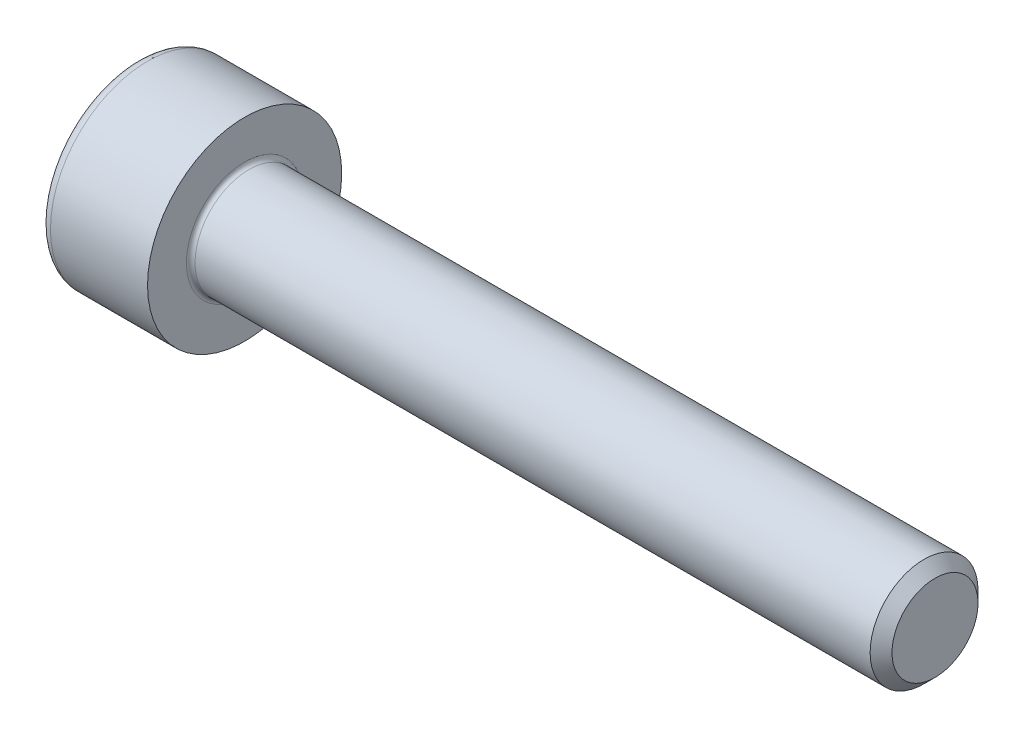
SolidWorks part; units mm, degrees
ref_plane "Plane1" through (0, 0, 0) normal (0, 0, 1) x (1, 0, 0)
ref_plane "Plane2" through (0, 0, 0) normal (0, 1, 0) x (1, 0, 0)
ref_plane "Plane3" through (0, 0, 0) normal (1, 0, 0) x (0, 0, -1)
sketch "BodySke" plane through (0, 0, 0) normal (0, 0, 1) x (1, 0, 0)
  line L0 (0, 0) -> (0, 2.25)
  line L1 (0, 2.25) -> (2.5, 2.25)
  line L2 (2.5, 2.25) -> (2.5, 1.25)
  line L3 (2.5, 1.25) -> (18.2465, 1.25)
  line L4 (18.5, 0.9965) -> (18.5, 0)
  line L5 (18.5, 0) -> (0, 0)
  line L6 (-31.75, 0) -> (127, 0) construction
  line L8 (18.5, 0.9965) -> (18.2465, 1.25)
  line L10 (18.5, -0.9965) -> (18.2465, -1.25) construction
  line L11 (2.95, 9.525) -> (2.95, 3.175) construction
  line L12 (2.5, 9.525) -> (2.5, 3.175) construction
  line L13 (-41.5, 9.525) -> (-41.5, 3.175) construction
  dimension "Diameter" = 2.5
  dimension "Head_ht" = 2.5
  dimension "Length" = 16
  dimension "Body_ch_ang" = 45
  dimension "Head_dia" = 4.5
  dimension "Minor_dia" = 1.993
  dimension "Advance" = 0.45
  dimension "Thread_nom" = 16
  dimension "Thread_length" = 60
revolve "Base-Revolve" add sketch "BodySke"
cosmetic thread "ThreadCosmetic"
fillet "Fillet1" radius 0.1 1 edges at (2.5, 0, 1.25)
fillet "Fillet2" radius 0.25 1 edges at (0, 0, 2.25)
sketch "Sketch2" plane through (0, 0, 0) normal (0, 0, 1) x (1, 0, 0)
  line L0 (0, 1.01) -> (1.1, 1.01)
  line L1 (1.1, 1.01) -> (1.6831, 0)
  line L2 (-31.75, 0) -> (127, 0) construction
  line L3 (1.6831, 0) -> (0, 0)
  line L4 (0, 0) -> (0, 1.01)
  line L6 (0, 0) -> (47.625, 0) construction
  dimension "D1" = 1.01
  dimension "D2" = 60
  dimension "Depth" = 1.1
revolve "Hex-PreBroach" cut sketch "Sketch2" angle 360 about L6
sketch "Sketch3" plane through (0, 0, 0) normal (-1, 0, 0) x (0, 0.5, 0.866)
  line L0 (0.5831, 1.01) -> (-0.5831, 1.01)
  line L1 (-0.5831, 1.01) -> (-1.1662, 0)
  line L2 (0.5831, 1.01) -> (1.1662, 0)
  line L3 (0.5831, -1.01) -> (1.1662, 0)
  line L4 (0.5831, -1.01) -> (-0.5831, -1.01)
  line L5 (-0.5831, -1.01) -> (-1.1662, 0)
  dimension "D1" = 1.01
  dimension "D2" = 1.01
  dimension "Hex_size" = 2.02
extrude "Hex" cut sketch "Sketch3" against normal blind 1.1
sketch "ThdSchSke" plane through (0, 0, 0) normal (0, 0, 1) x (1, 0, 0)
  line L0 (3.85, -0.9965) -> (3.6725, -1.25)
  line L1 (3.85, -0.9965) -> (4.0275, -1.25)
  line L2 (4.0275, -1.25) -> (4.0275, -1.5625)
  line L3 (-3.175, 0) -> (5.1513, 0) construction
  line L4 (0, 2) -> (0, -2) construction
  line L5 (4.0275, -1.5625) -> (3.6725, -1.5625)
  line L6 (3.6725, -1.5625) -> (3.6725, -1.25)
  dimension "Thread_minor" = 1.993
  dimension "Diameter" = 2.5
  dimension "Start" = 3.85
  dimension "SideAngle" = 55
  dimension "VeeAngle" = 70
  dimension "Overcut" = 3.125
revolve "ThreadSchematic" [suppressed] cut sketch "ThdSchSke" angle 360 about L3
pattern_linear "ThdSchPat" [suppressed]
equation "\"D2@Sketch3\" = \"Hex_size@Sketch3\" / 2"
equation "\"D1@Sketch3\" = \"Hex_size@Sketch3\" / 2"
equation "\"D1@Sketch2\" = \"Hex_size@Sketch3\" / 2"
equation "\"Thread_minor@ThreadCosmetic\"  =  \"Minor_dia@BodySke\""
equation "\"Depth@Sketch2\" =  \"Key_eng@Hex\""
equation "\"Thread_length@ThreadCosmetic\" = ((sgn( (\"Length@BodySke\" - \"Advance@BodySke\" * 3.0) - \"Thread_nom@BodySke\" )-1)*( (\"Length@BodySke\" - \"Advance@BodySke\" * 3.0) - \"Thread_nom@BodySke\" ))/-2+ \"Thread_nom@BodySke\""
equation "\"Thread_minor@ThdSchSke\" = \"Minor_dia@BodySke\""
equation "\"Diameter@ThdSchSke\" = \"Diameter@BodySke\""
equation "\"Overcut@ThdSchSke\" = \"Diameter@BodySke\" * 1.25"
equation "\"Start@ThdSchSke\" = \"Head_ht@BodySke\" + \"Length@BodySke\" - \"Thread_length@ThreadCosmetic\"  '---Non-countersunk---"
equation "\"Num_threads@ThdSchPat\" = int( \"Thread_length@ThreadCosmetic\" / \"Advance@BodySke\" + 0.999 )  + 1"
equation "\"Advance@ThdSchPat\" = \"Thread_length@ThreadCosmetic\" /  (\"Num_threads@ThdSchPat\" - 1) 'relax it"
equation "\"Num_threads@ThdSchPat\" = \"Num_threads@ThdSchPat\" - sgn( \"Num_threads@ThdSchPat\" - 1) '---chamfered tips only---"
